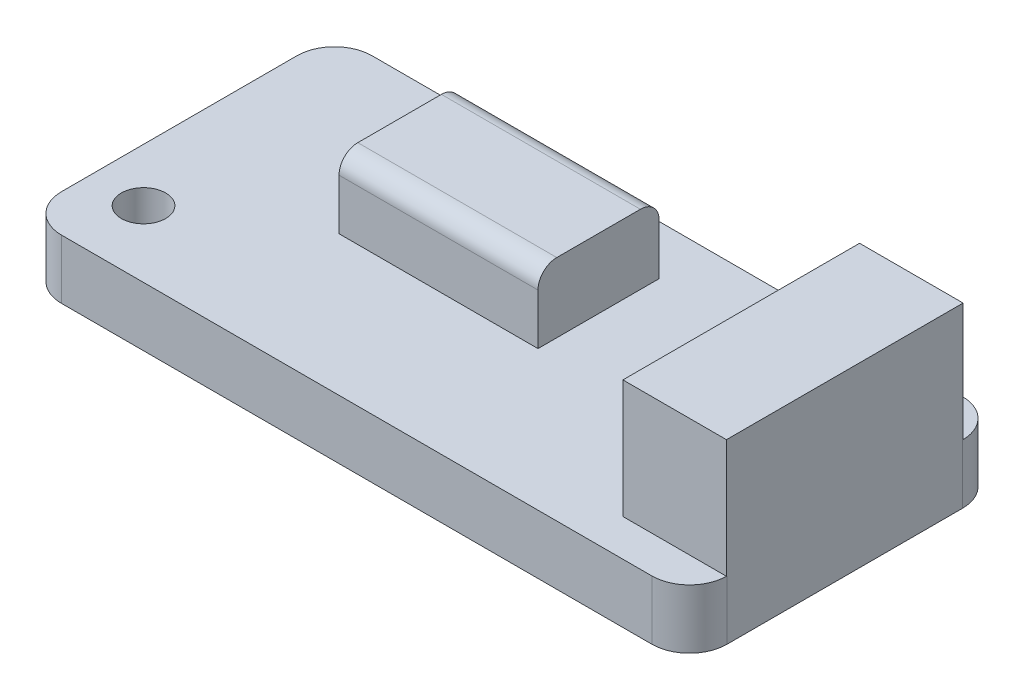
SolidWorks part; units mm, degrees
ref_plane "Front Plane" through (0, 0, 0) normal (0, 0, 1) x (1, 0, 0)
ref_plane "Top Plane" through (0, 0, 0) normal (0, 1, 0) x (1, 0, 0)
ref_plane "Right Plane" through (0, 0, 0) normal (1, 0, 0) x (0, 0, -1)
sketch "Sketch1" plane through (0, 0, 0) normal (0, 1, 0) x (1, 0, 0)
  line L1 (-19.96, -10.5) -> (19.96, -10.5)
  line L2 (-22.5, -7.96) -> (-22.5, 7.96)
  line L3 (-19.96, 10.5) -> (19.96, 10.5)
  line L4 (22.5, -7.96) -> (22.5, 7.96)
  line L5 (-22.5, -10.5) -> (22.5, 10.5) construction
  line L6 (-22.5, 10.5) -> (22.5, -10.5) construction
  arc A0 (19.96, 10.5) -> (22.5, 7.96) centre (19.96, 7.96) cw
  arc A1 (19.96, -10.5) -> (22.5, -7.96) centre (19.96, -7.96) ccw
  arc A2 (-19.96, -10.5) -> (-22.5, -7.96) centre (-19.96, -7.96) cw
  arc A3 (-22.5, 7.96) -> (-19.96, 10.5) centre (-19.96, 7.96) cw
  point P0 (0, 0)
  dimension "D3" = 2.54
  dimension "D1" = 45
  dimension "D2" = 21
extrude "Boss-Extrude1" add sketch "Sketch1" along normal blind 4
sketch "Sketch2" plane through (0, 4, 0) normal (0, 1, 0) x (1, 0, 0)
  line L0 (-22.5, 0) -> (22.5, 0) construction
  line L1 (22.5, -7.96) -> (22.5, 7.96) construction
  line L3 (15.5, -8) -> (22.5, -8)
  line L4 (15.5, -8) -> (15.5, 8)
  line L5 (15.5, 8) -> (22.5, 8)
  line L6 (22.5, -8) -> (22.5, 8)
  line L7 (15.5, -8) -> (22.5, 8) construction
  line L8 (15.5, 8) -> (22.5, -8) construction
  point P0 (19, 0)
  point P6 (0, 0)
  dimension "D1" = 16
  dimension "D2" = 7
  dimension "D3" = 0
extrude "Boss-Extrude2" add sketch "Sketch2" along normal blind 8
sketch "Sketch3" plane through (0, 4, 0) normal (0, 1, 0) x (1, 0, 0)
  line L1 (-10.6548, 7.1542) -> (2.7975, 7.1542)
  line L2 (-10.6548, 7.1542) -> (-10.6548, -1.0395)
  line L3 (-10.6548, -1.0395) -> (2.7975, -1.0395)
  line L4 (2.7975, 7.1542) -> (2.7975, -1.0395)
extrude "Boss-Extrude3" add sketch "Sketch3" along normal blind 4.698
fillet "Fillet1" radius 1.27 2 edges at (-3.9287, 8.698, -7.1542) (-3.9287, 8.698, 1.0395)
sketch "Sketch4" plane through (0, 4, 0) normal (0, 1, 0) x (1, 0, 0)
  line L1 (-18.902, -6.01) -> (10.308, -6.01) construction
  line L2 (-18.902, -6.01) -> (-18.902, 6.69) construction
  line L3 (-18.902, 6.69) -> (10.308, 6.69) construction
  line L4 (10.308, -6.01) -> (10.308, 6.69) construction
  line L5 (-18.902, -6.01) -> (10.308, 6.69) construction
  line L6 (-18.902, 6.69) -> (10.308, -6.01) construction
  line L7 (22.5, -7.96) -> (22.5, 7.96) construction
  line L8 (19.96, 10.5) -> (-19.96, 10.5) construction
  circle A4 centre (-18.902, -6.01) radius 1.5
  circle A5 centre (10.308, 6.69) radius 1.5
  point P0 (-4.297, 0.34)
  dimension "D5" = 3
  dimension "D6" = 3
  dimension "D1" = 29.21
  dimension "D2" = 12.7
  dimension "D3" = 3.81
  dimension "D4" = 12.192
extrude "Cut-Extrude1" cut sketch "Sketch4" against normal through all
